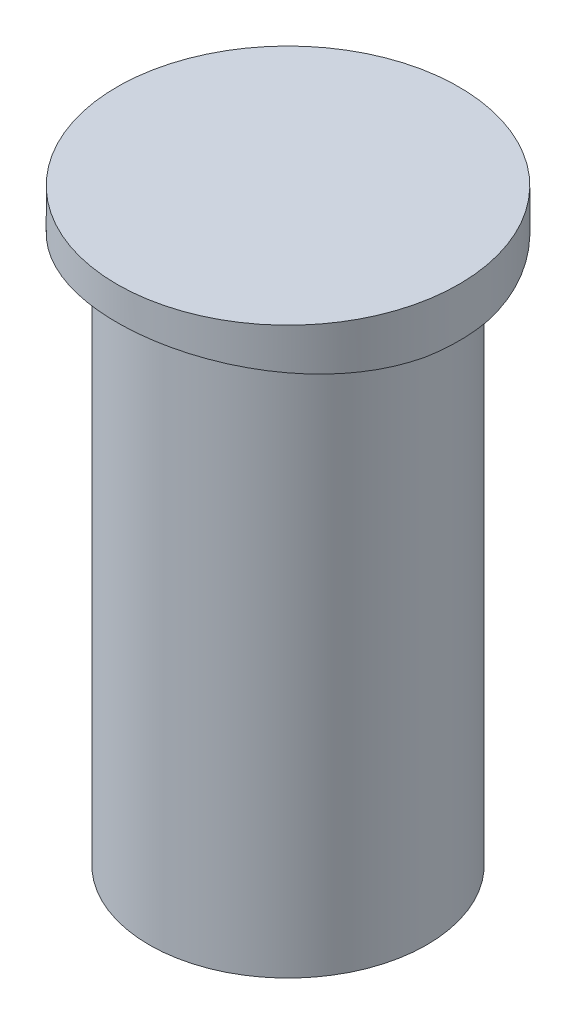
SolidWorks part; units mm, degrees
ref_plane "Front Plane" through (0, 0, 0) normal (0, 0, 1) x (1, 0, 0)
ref_plane "Top Plane" through (0, 0, 0) normal (0, 1, 0) x (1, 0, 0)
ref_plane "Right Plane" through (0, 0, 0) normal (1, 0, 0) x (0, 0, -1)
sketch "Sketch1" plane through (0, 0, 0) normal (0, 1, 0) x (1, 0, 0)
  circle A0 centre (0, 0) radius 6.1849
extrude "Boss-Extrude1" add sketch "Sketch1" along normal blind 23.9776
sketch "Sketch2" plane through (0, 23.9776, 0) normal (0, 1, 0) x (1, 0, 0)
  circle A0 centre (0, 0) radius 7.62
extrude "Boss-Extrude2" add sketch "Sketch2" along normal blind 2.2352
sketch "Sketch4" plane through (0, 23.9776, 0) normal (0, -1, 0) x (1, 0, 0)
  circle A0 centre (0, 0) radius 7.62
  circle A1 centre (0, 0) radius 6.1849
extrude "Cut-Extrude2" cut sketch "Sketch4" against normal blind 0.0254 and the other way through all
sketch "Sketch8" plane through (0, 0, 0) normal (0, 0, 1) x (1, 0, 0)
  line L1 (-7.6015, 24.0084) -> (7.6015, 24.0084)
  arc A1 (7.6015, 24.0084) -> (-7.6015, 24.0084) centre (0, -15.1384) ccw
extrude "Cut-Extrude3" cut sketch "Sketch8" against normal through all both and the other way through all
sketch "Sketch9" plane through (0, 24.003, 0) normal (0, -1, 0) x (1, 0, 0)
  circle A0 centre (0, 0) radius 6.1849
  circle A1 centre (0, 0) radius 7.62
extrude "Cut-Extrude4" cut sketch "Sketch9" against normal blind 0.0254 and the other way through all
